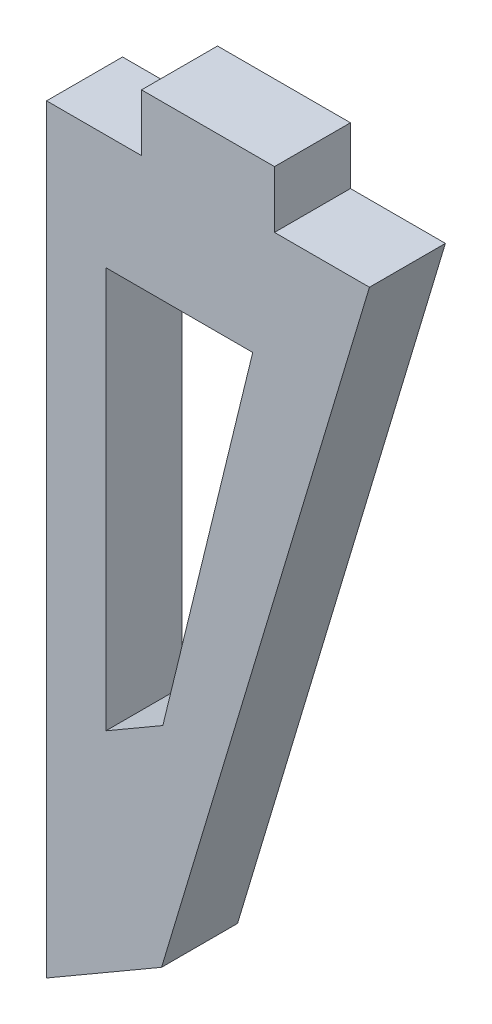
SolidWorks part; units mm, degrees
ref_plane "Front Plane" through (0, 0, 0) normal (0, 0, 1) x (1, 0, 0)
ref_plane "Top Plane" through (0, 0, 0) normal (0, 1, 0) x (1, 0, 0)
ref_plane "Right Plane" through (0, 0, 0) normal (1, 0, 0) x (0, 0, -1)
sketch "Sketch1" plane through (0, 0, 0) normal (0, 0, 1) x (1, 0, 0)
  line L0 (0, 0) -> (-8.5, 0) construction
  line L1 (-8.5, 0) -> (-8.5, -20) construction
  line L2 (-8.5, -20) -> (-6, -20) construction
  line L3 (-6, -20) -> (0, 0) construction
  line L4 (-2.5, 0) -> (-6, 0) construction
  line L5 (-6, 0) -> (-6, 1.5) construction
  line L6 (-6, 1.5) -> (-2.5, 1.5) construction
  line L7 (-2.5, 1.5) -> (-2.5, 0) construction
  line L8 (-8.5, -20) -> (-5.4729, -18.2431) construction
  line L9 (-8.5, 0) -> (-8.5, -20)
  line L10 (-8.5, -20) -> (-5.4729, -18.2431)
  line L11 (-5.4729, -18.2431) -> (0, 0)
  line L12 (0, 0) -> (-2.5, 0)
  line L13 (-2.5, 0) -> (-2.5, 1.5)
  line L14 (-2.5, 1.5) -> (-6, 1.5)
  line L15 (-6, 1.5) -> (-6, 0)
  line L16 (-6, 0) -> (-8.5, 0)
  line L17 (-3.4394, -4.5236) -> (-5.4394, -12.7131)
  line L23 (-4.4394, -7.6397) -> (-6.9394, -8.8397) construction
  line L24 (-4.4394, -8.8397) -> (-6.9394, -7.6397) construction
  line L28 (-3.4394, -3.0236) -> (-6.9394, -3.0236)
  line L29 (-6.9394, -4.5236) -> (-6.9394, -3.0236)
  line L30 (-3.4394, -4.5236) -> (-6.9394, -3.0236) construction
  line L31 (-3.4394, -3.0236) -> (-6.9394, -4.5236) construction
  line L33 (-6.9394, -11.7131) -> (-6.9394, -12.7131)
  line L34 (-5.4394, -11.7131) -> (-6.9394, -12.7131) construction
  line L35 (-5.4394, -12.7131) -> (-6.9394, -11.7131) construction
  line L36 (-6.9394, -11.7131) -> (-6.9394, -4.5236)
  line L37 (-3.4394, -4.5236) -> (-3.073, -3.0236)
  line L38 (-3.073, -3.0236) -> (-3.4394, -3.0236)
  line L39 (-5.4394, -12.7131) -> (-6.9394, -13.5837)
  line L40 (-6.9394, -12.7131) -> (-6.9394, -13.5837)
  point P8 (-4.25, 0)
  point P11 (-6.1894, -12.2131)
  point P12 (-5.6894, -8.2397)
  point P17 (-5.1894, -3.7736)
  dimension "D1" = 8.5
  dimension "D2" = 20
  dimension "D3" = 2.5
  dimension "D4" = 3.5
  dimension "D5" = 1.5
  dimension "D6" = 3.5
  dimension "D7" = 1.2
  dimension "D8" = 2.5
  dimension "D9" = 1.5
  dimension "D10" = 3.5
  dimension "D11" = 1
  dimension "D12" = 1.5
extrude "Boss-Extrude1" add sketch "Sketch1" along normal blind 2
sketch "Sketch2" plane through (0, 0, 2) normal (0, 0, 1) x (1, 0, 0)
  line L0 (-8.5, -20) -> (-8.5, -32)
  line L1 (-8.5, -32) -> (-5.4729, -18.2431)
  dimension "D1" = 12
  dimension "D2" = 14.086
